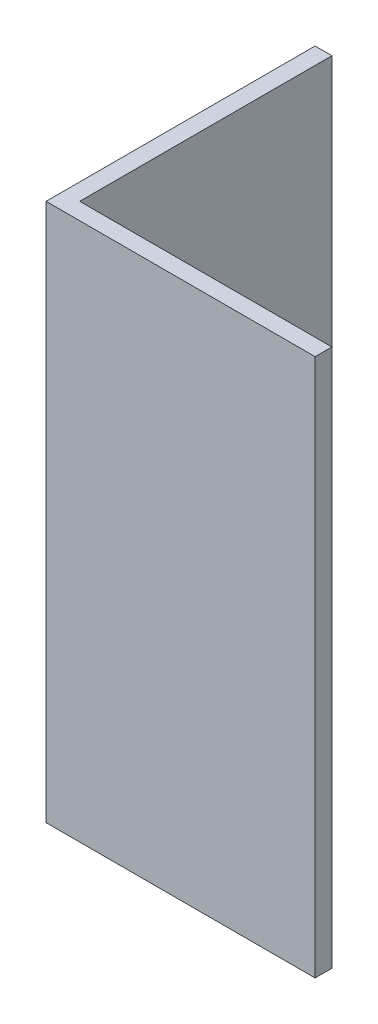
SolidWorks part; units mm, degrees
material "6061-T6 (SS)"
ref_plane "Front Plane" through (0, 0, 0) normal (0, 0, 1) x (1, 0, 0)
ref_plane "Top Plane" through (0, 0, 0) normal (0, 1, 0) x (1, 0, 0)
ref_plane "Right Plane" through (0, 0, 0) normal (1, 0, 0) x (0, 0, -1)
sketch "Sketch1" plane through (0, 0, 0) normal (0, 1, 0) x (1, 0, 0)
  line L0 (0, 0) -> (0, 25.4)
  line L1 (0, 25.4) -> (1.5875, 25.4)
  line L2 (1.5875, 25.4) -> (1.5875, 1.5875)
  line L3 (1.5875, 1.5875) -> (25.4, 1.5875)
  line L4 (25.4, 1.5875) -> (25.4, 0)
  line L5 (25.4, 0) -> (0, 0)
  dimension "D1" = 1.5875
  dimension "D2" = 25.4
extrude "Boss-Extrude1" add sketch "Sketch1" along normal blind 50.8
